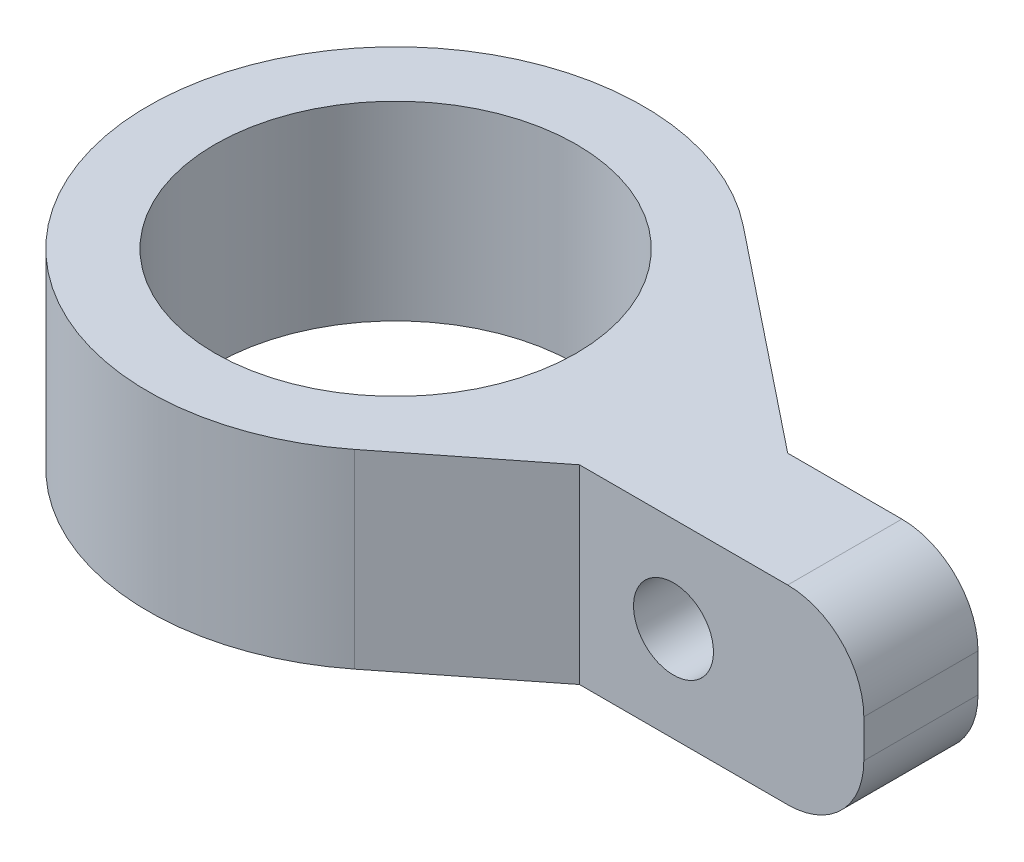
SolidWorks part; units mm, degrees
ref_plane "Front Plane" through (0, 0, 0) normal (0, 0, 1) x (1, 0, 0)
ref_plane "Top Plane" through (0, 0, 0) normal (0, 1, 0) x (1, 0, 0)
ref_plane "Right Plane" through (0, 0, 0) normal (1, 0, 0) x (0, 0, -1)
sketch "Sketch1" plane through (0, 0, 0) normal (0, 0, 1) x (1, 0, 0)
  line L1 (5, -2.5) -> (-5, -2.5)
  line L2 (5, -2.5) -> (5, 2.5)
  line L3 (5, 2.5) -> (-5, 2.5)
  line L4 (-5, -2.5) -> (-5, 2.5)
  line L5 (5, -2.5) -> (-5, 2.5) construction
  line L6 (5, 2.5) -> (-5, -2.5) construction
  point P0 (0, 0)
  dimension "D1" = 10
  dimension "D2" = 5
extrude "Boss-Extrude1" add sketch "Sketch1" along normal blind 3
fillet "Fillet1" radius 2 2 edges at (5, -2.5, 1.5) (5, 2.5, 1.5)
sketch "Sketch3" plane through (0, 0, 0) normal (0, 1, 0) x (1, 0, 0)
  line L0 (-5, -3) -> (-5, 0) construction
  line L1 (-5, 0) -> (3, 0) construction
  circle A0 centre (-9.8, -0.5) radius 6.5
  dimension "D2" = 13
  dimension "D1" = 4.8
  dimension "D3" = 0.5
extrude "Boss-Extrude2" add sketch "Sketch3" along normal mid plane 5 separate body
sketch "Sketch4" plane through (0, -2.5, 0) normal (0, -1, 0) x (1, 0, 0)
  line L1 (-5, 3) -> (-5, 0) construction
  circle A1 centre (-9.8, 0.5) radius 4.75
  circle A2 centre (-9.8, 0.5) radius 6.5 construction
  dimension "D1" = 9.5
  dimension "D3" = 0
  dimension "D2" = 4.8
extrude "Cut-Extrude1" cut sketch "Sketch4" against normal through all
sketch "Sketch7" plane through (0, 0, 3) normal (0, 0, 1) x (1, 0, 0)
  circle A0 centre (0, 0) radius 1.05
  dimension "D1" = 2.1
extrude "Cut-Extrude2" cut sketch "Sketch7" against normal blind 2
sketch "Sketch8" plane through (0, -2.5, 0) normal (0, -1, 0) x (1, 0, 0)
  line L0 (-5.7771, 5.6055) -> (-2.4704, 3)
  line L1 (-5, 3) -> (3, 3) construction
  line L2 (-2.4704, 3) -> (-3.8, 3)
  line L3 (-5.7481, -4.5825) -> (0, 0)
  line L4 (0, 0) -> (-3.3193, 0)
  circle A0 centre (-9.8, 0.5) radius 6.5 construction
  arc A1 (-5.7771, 5.6055) -> (-3.8, 3) centre (-9.8, 0.5) cw
  arc A2 (-3.3193, 0) -> (-5.7481, -4.5825) centre (-9.8, 0.5) cw
extrude "Boss-Extrude3" add sketch "Sketch8" against normal up to surface (5 mm away) up to face at (-9.8, 2.5, -4.25)
